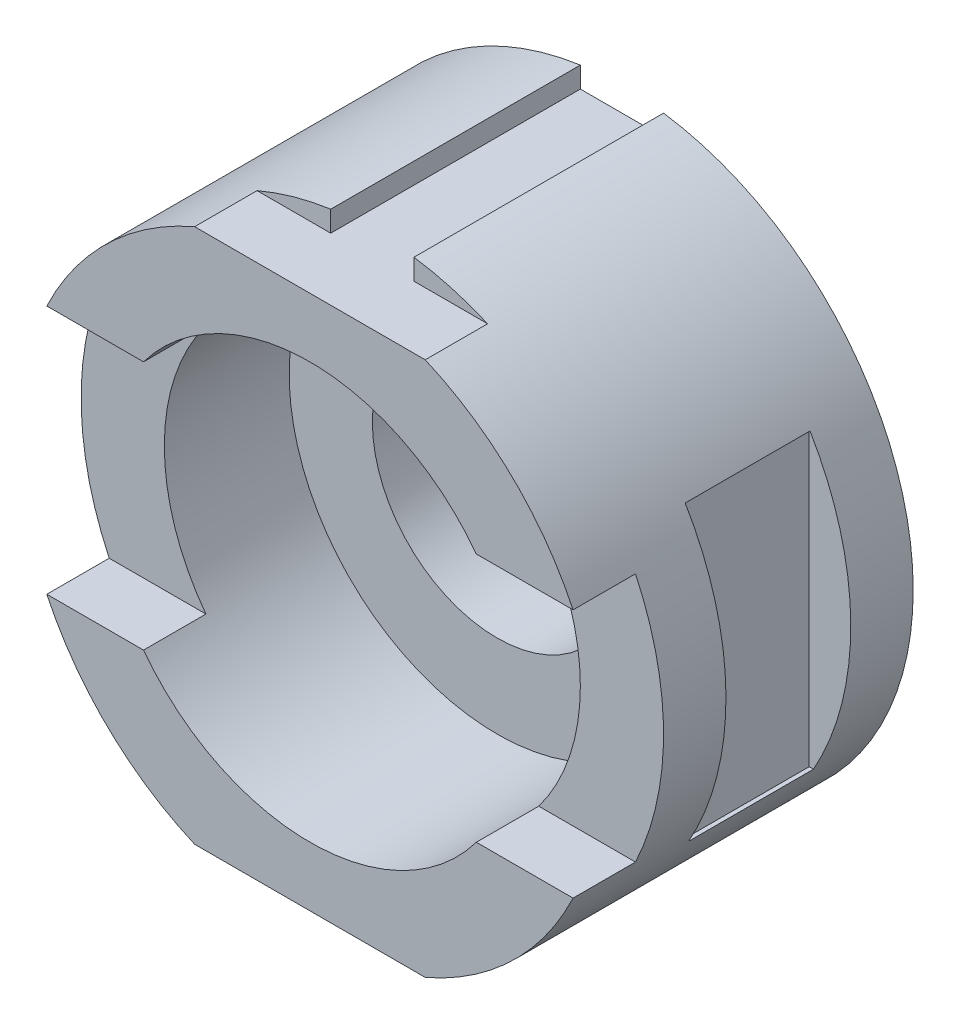
SolidWorks part; units mm, degrees
ref_plane "Front Plane" through (0, 0, 0) normal (0, 0, 1) x (1, 0, 0)
ref_plane "Top Plane" through (0, 0, 0) normal (0, 1, 0) x (1, 0, 0)
ref_plane "Right Plane" through (0, 0, 0) normal (1, 0, 0) x (0, 0, -1)
sketch "Sketch1" plane through (0, 0, 0) normal (0, 0, 1) x (1, 0, 0)
  circle A0 centre (0, 0) radius 70
  dimension "D1" = 140
extrude "Boss-Extrude1" add sketch "Sketch1" along normal blind 75
sketch "Sketch2" plane through (0, 0, 75) normal (0, 0, 1) x (1, 0, 0)
  circle A0 centre (0, 0) radius 30
  dimension "D1" = 60
extrude "Cut-Extrude1" cut sketch "Sketch2" against normal blind 75
sketch "Sketch3" plane through (0, 0, 75) normal (0, 0, 1) x (1, 0, 0)
  line L0 (-10, 69.282) -> (10, 69.282)
  arc A0 (10, 69.282) -> (-10, 69.282) centre (0, 0) ccw
  circle A1 centre (0, 0) radius 70 construction
  circle M2 centre (0, 0) radius 70
  dimension "D1" = 20
  dimension "D2" = 0
extrude "Cut-Extrude2" cut sketch "Sketch3" against normal blind 75 contours L0 M2
sketch "Sketch4" plane through (0, 0, 75) normal (0, 0, 1) x (1, 0, 0)
  line L0 (10, -69.282) -> (-10, -69.282)
  arc A0 (10, -69.282) -> (-10, -69.282) centre (0, 0) cw
  arc A1 (-10, 69.282) -> (10, 69.282) centre (0, 0) ccw construction
  arc M2 (-10, 69.282) -> (10, 69.282) centre (0, 0) ccw
  dimension "D1" = 20
  dimension "D2" = 10
  dimension "D3" = 0
extrude "Cut-Extrude3" cut sketch "Sketch4" against normal blind 75 contours L0 M2
ref_plane "Plane1" through (-60, 0, 0) normal (1, 0, 0) x (0, 0, -1)
sketch "Sketch5" plane through (-60, 0, 0) normal (1, 0, 0) x (0, 0, -1)
  line L0 (0, -69.282) -> (0, 69.282) construction
  line L1 (-15, 35.718) -> (-45, 35.718)
  line L2 (-15, 35.718) -> (-15, -34.282)
  line L3 (-15, -34.282) -> (-45, -34.282)
  line L4 (-45, 35.718) -> (-45, -34.282)
  line L5 (0, -69.282) -> (-75, -69.282) construction
  dimension "D1" = 30
  dimension "D2" = 15
  dimension "D3" = 70
  dimension "D4" = 35
extrude "Cut-Extrude5" cut sketch "Sketch5" against normal blind 75
ref_plane "Plane2" through (60, 0, 0) normal (1, 0, 0) x (0, 0, -1)
sketch "Sketch6" plane through (60, 0, 0) normal (1, 0, 0) x (0, 0, -1)
  line L0 (0, -69.282) -> (0, 69.282) construction
  line L1 (-45, 35.718) -> (-15, 35.718)
  line L2 (-45, 35.718) -> (-45, -34.282)
  line L3 (-45, -34.282) -> (-15, -34.282)
  line L4 (-15, 35.718) -> (-15, -34.282)
  dimension "D1" = 30
  dimension "D2" = 15
  dimension "D3" = 35
  dimension "D4" = 70
extrude "Cut-Extrude6" cut sketch "Sketch6" along normal blind 75
sketch "Sketch7" plane through (0, 69.282, 0) normal (0, 1, 0) x (1, 0, 0)
  line L1 (25, -75) -> (-25, -75)
  line L2 (25, -75) -> (25, -60)
  line L3 (25, -60) -> (-25, -60)
  line L4 (-25, -75) -> (-25, -60)
  dimension "D1" = 0
  dimension "D2" = 15
  dimension "D3" = 15
  dimension "D4" = 15
extrude "Cut-Extrude11" cut sketch "Sketch7" against normal blind 5
sketch "Sketch10" plane through (0, 0, 60) normal (0, 0, 1) x (1, 0, 0)
  line L0 (-10, 69.282) -> (-10, 64.282)
  line L1 (25, 64.282) -> (-25, 64.282) construction
  line L2 (-10, 64.282) -> (10.0717, 64.282)
  line L3 (10.0717, 64.282) -> (10, 69.282)
  line L4 (10, 69.282) -> (-10, 69.282)
extrude "Cut-Extrude12" cut sketch "Sketch10" against normal blind 88
sketch "Sketch12" plane through (-25, 0, 0) normal (1, 0, 0) x (0, 0, -1)
  line L1 (-60, 65.3835) -> (-75, 65.3835)
  line L2 (-60, 65.3835) -> (-60, 64.282)
  line L3 (-60, 64.282) -> (-75, 64.282)
  line L4 (-75, 65.3835) -> (-75, 64.282)
extrude "Cut-Extrude14" cut sketch "Sketch12" against normal blind 88
sketch "Sketch13" plane through (25, 0, 0) normal (-1, 0, 0) x (0, 0, 1)
  line L1 (60, 65.3835) -> (75, 65.3835)
  line L2 (60, 65.3835) -> (60, 64.282)
  line L3 (60, 64.282) -> (75, 64.282)
  line L4 (75, 65.3835) -> (75, 64.282)
extrude "Cut-Extrude15" cut sketch "Sketch13" against normal blind 88
sketch "Sketch14" plane through (0, -69.282, 0) normal (0, -1, 0) x (1, 0, 0)
  line L0 (70, 75) -> (10, 75) construction
  line L1 (-25, 75) -> (25, 75)
  line L2 (-25, 75) -> (-25, 60)
  line L3 (-25, 60) -> (25, 60)
  line L4 (25, 75) -> (25, 60)
  dimension "D1" = 15
  dimension "D2" = 15
  dimension "D3" = 15
  dimension "D4" = 0
extrude "Cut-Extrude16" cut sketch "Sketch14" against normal blind 5
sketch "Sketch15" plane through (0, 0, 60) normal (0, 0, 1) x (1, 0, 0)
  line L0 (-25, -64.282) -> (25, -64.282) construction
  line L1 (-10, -69.282) -> (10, -69.282)
  line L2 (-10, -69.282) -> (-10, -64.282)
  line L3 (-10, -64.282) -> (10, -64.282)
  line L4 (10, -69.282) -> (10, -64.282)
  dimension "D1" = 20
extrude "Cut-Extrude17" cut sketch "Sketch15" against normal blind 73
sketch "Sketch16" plane through (25, 0, 0) normal (-1, 0, 0) x (0, 0, 1)
  line L1 (60, -64.282) -> (75, -64.282)
  line L2 (60, -64.282) -> (60, -65.3835)
  line L3 (60, -65.3835) -> (75, -65.3835)
  line L4 (75, -64.282) -> (75, -65.3835)
extrude "Cut-Extrude18" cut sketch "Sketch16" against normal blind 73
sketch "Sketch17" plane through (-25, 0, 0) normal (1, 0, 0) x (0, 0, -1)
  line L1 (-75, -64.282) -> (-60, -64.282)
  line L2 (-75, -64.282) -> (-75, -65.3835)
  line L3 (-75, -65.3835) -> (-60, -65.3835)
  line L4 (-60, -64.282) -> (-60, -65.3835)
extrude "Cut-Extrude19" cut sketch "Sketch17" against normal blind 73
sketch "Sketch18" plane through (0, 0, 75) normal (0, 0, 1) x (1, 0, 0)
  line L0 (0, 30) -> (-63.2456, 30)
  line L1 (0, -30) -> (-63.2456, -30)
  line L2 (0, 30) -> (63.2456, 30)
  line L3 (0, -30) -> (63.2456, -30)
  arc A0 (0, 30) -> (0, -30) centre (0, 0) ccw
  circle A1 centre (0, 0) radius 30 construction
  arc A2 (0, 30) -> (0, -30) centre (0, 0) ccw
  arc A4 (-27.7096, 64.282) -> (-27.7096, -64.282) centre (0, 0) ccw construction
  arc A5 (27.7096, -64.282) -> (27.7096, 64.282) centre (0, 0) ccw construction
  arc A6 (-63.2456, 30) -> (-63.2456, -30) centre (0, 0) ccw
  arc A7 (63.2456, 30) -> (63.2456, -30) centre (0, 0) cw
  circle A8 centre (0, 0) radius 30
  arc M1 (-27.7096, 64.282) -> (-27.7096, -64.282) centre (0, 0) ccw
  arc M3 (27.7096, -64.282) -> (27.7096, 64.282) centre (0, 0) ccw
  circle M5 centre (0, 0) radius 30
  dimension "D1" = 30
  dimension "D2" = 30
  dimension "D3" = 30
  dimension "D4" = 30
extrude "Cut-Extrude20" cut sketch "Sketch18" against normal blind 15 contours L1 L0 M5 M1 | L3 L2 M5 M3
ref_plane "Plane3" through (0, 0, 75) normal (0, 0, 1) x (1, 0, 0)
sketch "Sketch20" plane through (0, 0, 75) normal (0, 0, 1) x (1, 0, 0)
  circle A0 centre (0, 0) radius 50
  dimension "D1" = 100
extrude "Cut-Extrude21" cut sketch "Sketch20" against normal blind 45
